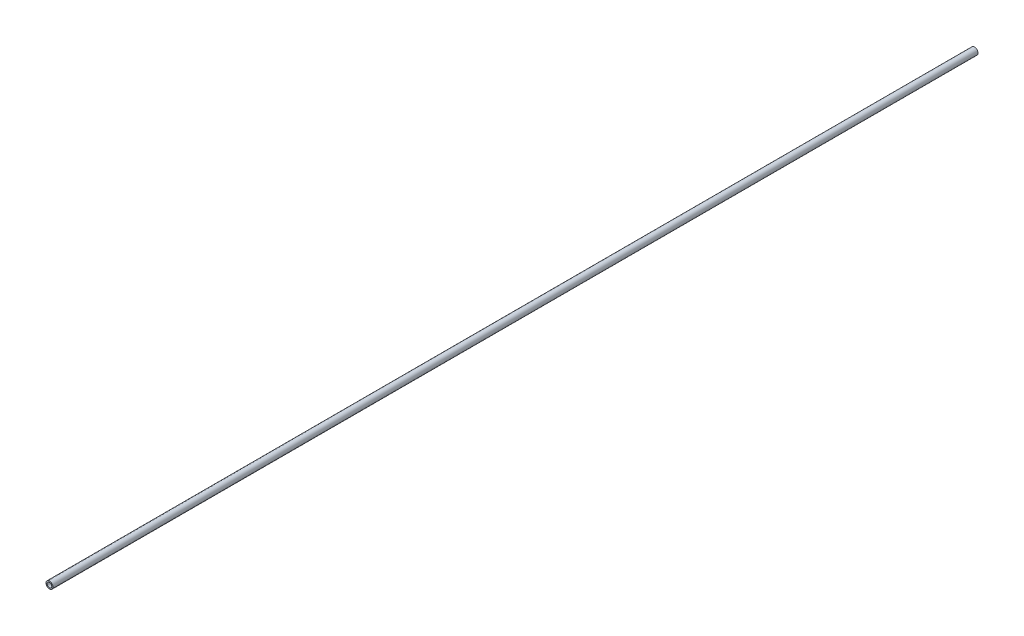
SolidWorks part; units mm, degrees
material "Carbon Fiber Tube - UD Approx"
ref_plane "Front Plane" through (0, 0, 0) normal (0, 0, 1) x (1, 0, 0)
ref_plane "Top Plane" through (0, 0, 0) normal (0, 1, 0) x (1, 0, 0)
ref_plane "Right Plane" through (0, 0, 0) normal (1, 0, 0) x (0, 0, -1)
sketch "Sketch1" plane through (0, 0, 0) normal (0, 0, 1) x (1, 0, 0)
  circle A0 centre (0, 0) radius 2
  circle A1 centre (0, 0) radius 3
  dimension "D1" = 4
  dimension "D2" = 6
extrude "Boss-Extrude1" add sketch "Sketch1" along normal blind 800
